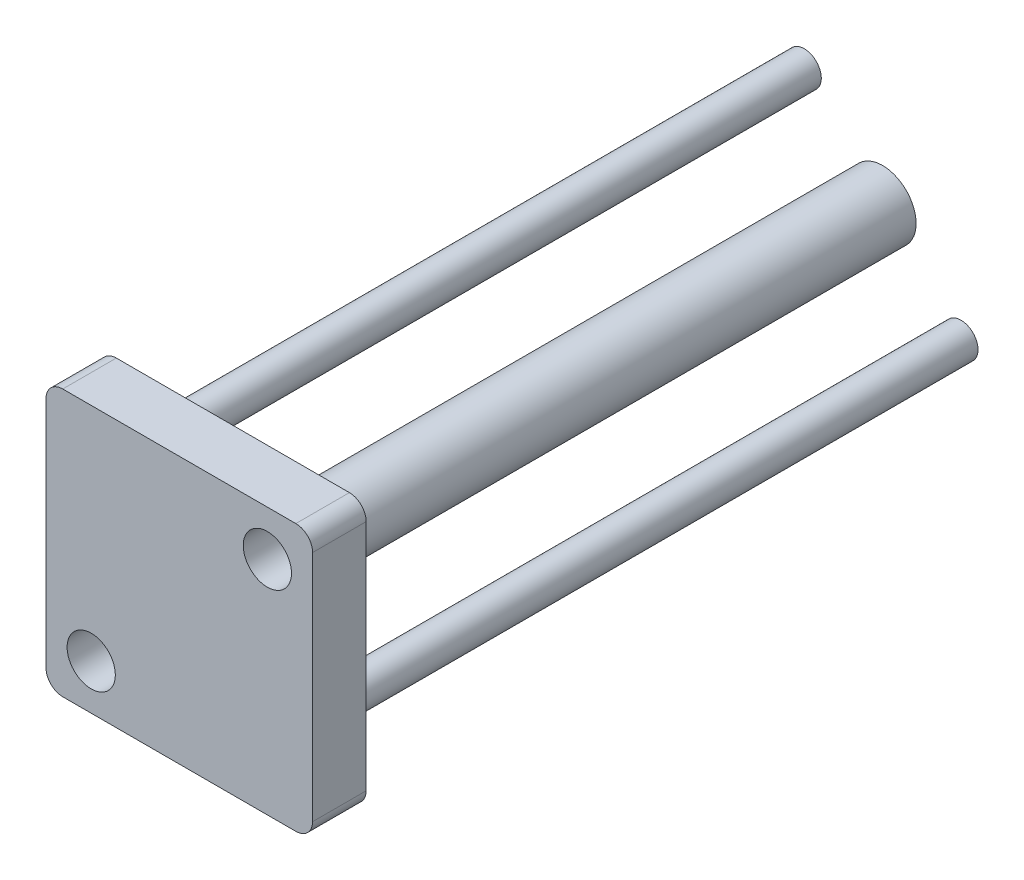
SolidWorks part; units mm, degrees
ref_plane "Front Plane" through (0, 0, 0) normal (0, 0, 1) x (1, 0, 0)
ref_plane "Top Plane" through (0, 0, 0) normal (0, 1, 0) x (1, 0, 0)
ref_plane "Right Plane" through (0, 0, 0) normal (1, 0, 0) x (0, 0, -1)
sketch "Sketch1" plane through (0, 0, 0) normal (0, 0, 1) x (1, 0, 0)
  circle A0 centre (0, 0) radius 5
  dimension "D1" = 10
extrude "Boss-Extrude1" add sketch "Sketch1" along normal blind 97
sketch "Sketch2" plane through (0, 0, 97) normal (0, 0, 1) x (1, 0, 0)
  line L1 (-17.4, -19.9) -> (17.4, -19.9)
  line L2 (-19.9, -17.4) -> (-19.9, 17.4)
  line L3 (-17.4, 19.9) -> (17.4, 19.9)
  line L4 (19.9, -17.4) -> (19.9, 17.4)
  arc A0 (-17.4, -19.9) -> (-19.9, -17.4) centre (-17.4, -17.4) cw
  arc A1 (-19.9, 17.4) -> (-17.4, 19.9) centre (-17.4, 17.4) cw
  arc A2 (17.4, 19.9) -> (19.9, 17.4) centre (17.4, 17.4) cw
  arc A3 (17.4, -19.9) -> (19.9, -17.4) centre (17.4, -17.4) ccw
  circle A5 centre (13.15, 13.15) radius 3.6
  circle A7 centre (-13.15, -13.15) radius 3.6
  point P0 (0, 0)
  point P4 (0, 19.9)
  point P6 (19.9, 0)
  point P11 (-19.9, 19.9)
  point P14 (19.9, 19.9)
  point P17 (19.9, -19.9)
  dimension "D3" = 2.5
  dimension "D4" = 2.5
  dimension "D5" = 7.2
  dimension "D1" = 39.8
  dimension "D2" = 39.8
  dimension "D6" = 6.75
  dimension "D7" = 6.75
  dimension "D8" = 6.75
  dimension "D9" = 6.75
extrude "Boss-Extrude2" add sketch "Sketch2" along normal blind 8
sketch "Sketch4" plane through (0, 0, 0) normal (0, 0, -1) x (-1, 0, 0)
  line L0 (19.9, 17.4) -> (19.9, -17.4) construction
  line L5 (-17.4, 19.9) -> (17.4, 19.9) construction
  line L6 (17.4, -19.9) -> (-17.4, -19.9) construction
  line L7 (-19.9, -17.4) -> (-19.9, 17.4) construction
  circle A0 centre (-11.7, -11.7) radius 2.55
  circle A1 centre (11.7, 11.7) radius 2.55
  dimension "D1" = 5.1
  dimension "D2" = 8.2
  dimension "D3" = 8.2
  dimension "D4" = 8.2
  dimension "D5" = 8.2
extrude "Boss-Extrude3" add sketch "Sketch4" against normal up to next
